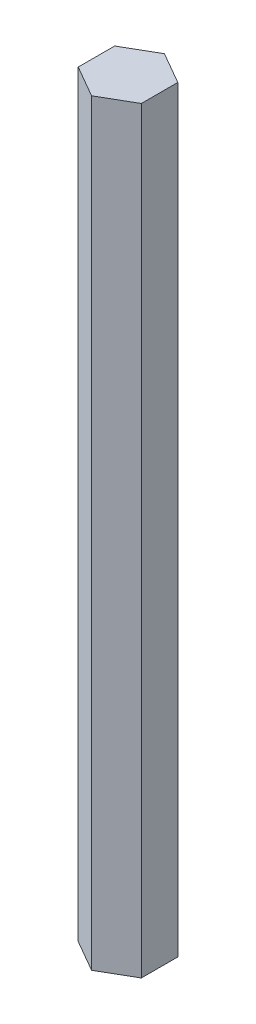
SolidWorks part; units mm, degrees
ref_plane "Front Plane" through (0, 0, 0) normal (0, 0, 1) x (1, 0, 0)
ref_plane "Top Plane" through (0, 0, 0) normal (0, 1, 0) x (1, 0, 0)
ref_plane "Right Plane" through (0, 0, 0) normal (1, 0, 0) x (0, 0, -1)
sketch "Sketch1" plane through (0, 0, 0) normal (0, 1, 0) x (1, 0, 0)
  line L1 (0, 5.7735) -> (-5, 2.8868)
  line L2 (-5, 2.8868) -> (-5, -2.8868)
  line L3 (-5, -2.8868) -> (0, -5.7735)
  line L4 (0, -5.7735) -> (5, -2.8868)
  line L5 (5, -2.8868) -> (5, 2.8868)
  line L6 (5, 2.8868) -> (0, 5.7735)
  circle A0 centre (0, 0) radius 5 construction
  dimension "D1" = 10
extrude "Boss-Extrude1" add sketch "Sketch1" along normal blind 120
sketch "Sketch2" plane through (0, 0, 0) normal (0, -1, 0) x (1, 0, 0)
  circle A0 centre (0, 0) radius 3
  dimension "D1" = 6
extrude "Cut-Extrude2" cut sketch "Sketch2" against normal blind 5
